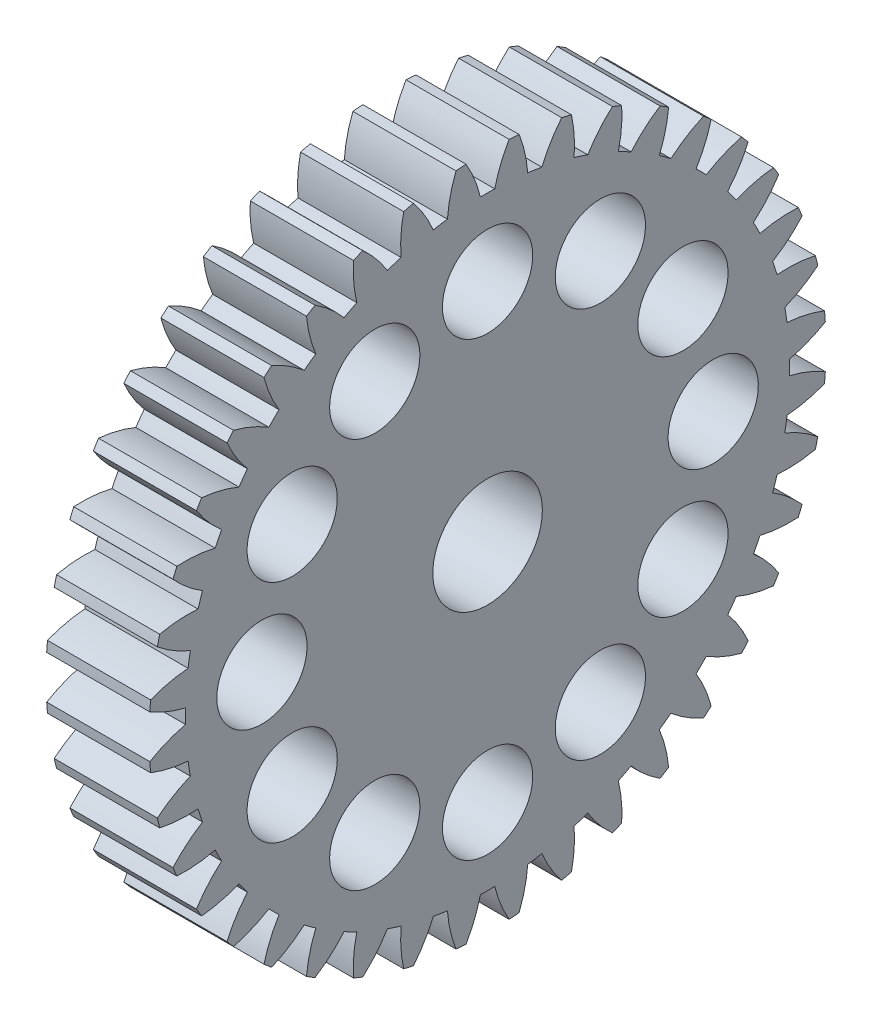
SolidWorks part; units mm, degrees
material "ПК/АБС"
ref_plane "Plane1" through (0, 0, 0) normal (0, 0, 1) x (1, 0, 0)
ref_plane "Plane2" through (0, 0, 0) normal (0, 1, 0) x (1, 0, 0)
ref_plane "Plane3" through (0, 0, 0) normal (1, 0, 0) x (0, 0, -1)
sketch "HoldingSke" plane through (0, 0, 0) normal (0, 1, 0) x (1, 0, 0)
  line L0 (0, 0) -> (0.6128, -0.5142)
  line L1 (-15, 0) -> (100, 0) construction
  line L2 (0, 0) -> (-2.1039, 2.3779)
  line L3 (0, 0) -> (-11.863, 4.5341)
  line L4 (0, 0) -> (6.6156, 5.5511)
  line L5 (0, 0) -> (-46.8476, -17.4728)
  line L6 (0, 0) -> (-6.6317, -4.4744)
  line L7 (-2.1039, 2.3779) -> (8.6586, 51.2059)
  line L8 (-76.2, 54.61) -> (-74.8, 54.61)
  line L9 (-71.009, 38.7566) -> (-53.1078, 45.2721)
  line L10 (-76.2, 71.12) -> (104.1128, 71.12)
  line L11 (0, 0) -> (-8, 0)
  line L12 (-76.2, 101.6) -> (-76.155, 101.6)
  line L13 (24.9733, 27.94) -> (52.9518, 28.4284)
  line L14 (24.9733, 27.94) -> (24.9743, 27.94)
  line L15 (24.9733, 27.94) -> (100.4006, 29.5858)
  line L16 (-63.627, -1.25) -> (-12.827, -1.25)
  circle A0 centre (0, 0) radius 4
  circle A1 centre (0, 0) radius 23.4365
  circle A2 centre (0, 0) radius 37.5
  circle A3 centre (0, 0) radius 4
  dimension "MHD" = 46.873
  dimension "Hub_dia" = 75
  dimension "Bore" = 8
  dimension "MBD" = 8
  dimension "Num_teeth" = 40
  dimension "Pitch" = 0.8
  dimension "Overall_len" = 50
  dimension "Show_teeth" = 40
  dimension "Thickness" = 8
  dimension "OAL" = 50.0001
  dimension "T_dim" = 1.4
  dimension "Ap" = 20
  dimension "H" = 19.05
  dimension "Pitch_radius" = 180.3128
  dimension "Width" = 8
  dimension "Backlash" = 0.045
  dimension "Addendum_fac" = 1
  dimension "Dedendum_fac" = 1.25
  dimension "Clearance_fac" = 0.25
  dimension "Dedendum_add" = 0.001
  dimension "Module" = 1.25
sketch "BasProSke" plane through (0, 0, 0) normal (0, 1, 0) x (1, 0, 0)
  line L0 (-10, 0) -> (60, 0) construction
  line L1 (0, 0) -> (0, 26.25)
  line L2 (0, 0) -> (8, 0)
  line L3 (8, 0) -> (8, 26.25)
  line L4 (8, 26.25) -> (0, 26.25)
  dimension "Thickness" = 8
  dimension "Diameter" = 52.5
revolve "Base-Revolve" add sketch "BasProSke" angle 360 about L0
sketch "TooCutSke" plane through (0, 0, 0) normal (1, 0, 0) x (0, 0, -1)
  line L1 (0, 0) -> (0, 107) construction
  line L2 (0, 0) -> (-1.0602, 24.9775) construction
  line L3 (0, 0) -> (-3.9204, 49.8134) construction
  line L4 (-1.0602, 24.9775) -> (-1.9602, 24.9067) construction
  arc A0 (0.5568, 23.4299) -> (-0.5568, 23.4299) centre (0, 0) ccw
  arc A1 (1.6852, 26.2213) -> (-1.6852, 26.2213) centre (0, 0) ccw
  circle A2 centre (0, 0) radius 25 construction
  circle A3 centre (0, 0) radius 23.4923 construction
  arc A4 (-0.5568, 23.4299) -> (-1.6852, 26.2213) centre (-10.2865, 21.1205) ccw
  arc A5 (1.6852, 26.2213) -> (0.5568, 23.4299) centre (10.2865, 21.1205) ccw
  dimension "Root_dia" = 46.873
  dimension "Overcut_dia" = 52.5508
  dimension "Pitch_dia" = 50
  dimension "Base_dia" = 46.9846
  dimension "Flank_rad" = 10
  dimension "Half_ang" = 4.5
  dimension "Half_CT" = 0.9027
extrude "ToothCut" cut sketch "TooCutSke" along normal through all
fillet "Breaks" [suppressed] radius 0.025
fillet "RootFillets" [suppressed] radius 0.3135
pattern_circular "TeethCuts" count 40 every 9 about axis through (-10, 0, 0) along (1, 0, 0) of "ToothCut", "RootFillets", "Breaks"
sketch "HubNeaOneSke" plane through (0, 0, 0) normal (-1, 0, 0) x (0, 0, 1)
  circle A0 centre (0, 0) radius 23.4365
  dimension "Diameter" = 46.873
extrude "HubNearOne" [suppressed] add sketch "HubNeaOneSke" along normal blind 42.0001
sketch "HubNeaBotSke" plane through (0, 0, 0) normal (-1, 0, 0) x (0, 0, 1)
  circle A0 centre (0, 0) radius 23.4365
  dimension "Diameter" = 46.873
extrude "HubNearBoth" [suppressed] add sketch "HubNeaBotSke" along normal blind 21
ref_plane "FarPln" through (8, 0, 0) normal (1, 0, 0) x (0, 0, -1)
sketch "HubFarSke" plane through (8, 0, 0) normal (1, 0, 0) x (0, 0, -1)
  circle A0 centre (0, 0) radius 23.4365
  dimension "Diameter" = 46.873
extrude "HubFar" [suppressed] add sketch "HubFarSke" along normal blind 21
sketch "BorSke" plane through (0, 0, 0) normal (1, 0, 0) x (0, 0, -1)
  circle A0 centre (0, 0) radius 4
  dimension "Diameter" = 8
extrude "Bore" cut sketch "BorSke" along normal mid plane 100.0001
sketch "KeySke" plane through (0, 0, 0) normal (1, 0, 0) x (0, 0, -1)
  line L0 (-1.5, 0) -> (-1.5, 5.4)
  line L1 (-1.5, 5.4) -> (1.5, 5.4)
  line L2 (1.5, 5.4) -> (1.5, 0)
  line L3 (0, 0) -> (0, 34) construction
  line L4 (-1.5, 0) -> (1.5, 0)
  dimension "Offset" = 5.4
  dimension "Width" = 3
extrude "Keyway" [suppressed] cut sketch "KeySke" along normal mid plane 100.0001
pattern_circular "Keyway2" [suppressed] count 2 every 90 about axis through (-10, 0, 0) along (1, 0, 0)
sketch "Эскиз1" plane through (8, 0, 0) normal (1, 0, 0) x (0, 0, -1)
  line L0 (0, 0) -> (0, 21) construction
  circle A0 centre (0, 0) radius 14
  circle A1 centre (0, 17.5) radius 3.5
  circle A2 centre (0, 0) radius 21
  point P6 (0, 0)
  dimension "D1" = 28
  dimension "D2" = 42
extrude "Вырез-Вытянуть1" cut sketch "Эскиз1" against normal through all both and the other way through all contours L0 A1 | A1 L0
pattern_circular "Круговой массив1" count 12 every 30 about axis through (0, 0, 0) along (1, 0, 0) of "Вырез-Вытянуть1"
sketch "Эскиз2" plane through (8, 0, 0) normal (1, 0, 0) x (0, 0, -1)
  circle A0 centre (0, 0) radius 4.25
  dimension "D1" = 8.5
extrude "Вырез-Вытянуть2" cut sketch "Эскиз2" against normal blind 10
equation "' \"Module@HoldingSke\" = 6.35"
equation "' \"Num_teeth@HoldingSke\" = 12"
equation "' \"Ap@HoldingSke\" =  20"
equation "' \"Ap@HoldingSke\" = 20"
equation "' \"Width@HoldingSke\" = 0.5 * 25.4"
equation "' \"Hub_dia@HoldingSke\"= 1 * 25.4"
equation "' \"Hub_dia@HoldingSke\" = 1 * 25.4"
equation "' \"Overall_len@HoldingSke\" = 1.0 * 25.4"
equation "' \"Bore@HoldingSke\" = 0.75 * 25.4"
equation "' \"T_dim@HoldingSke\" = 0.1 * 25.4"
equation "' \"Width@KeySke\" = 0.25 * 25.4"
equation "' \"Show_teeth@HoldingSke\" = 13"
equation "' \"Backlash@HoldingSke\" = 0.009 * 25.4"
equation "' \"Addendum_fac@HoldingSke\" = 1.0"
equation "' \"Dedendum_fac@HoldingSke\" = 1.25"
equation "' \"Dedendum_add@HoldingSke\" = 0.00005 * 25.4"
equation "' \"Clearance_fac@HoldingSke\" = 0.25"
equation "\"Pitch@HoldingSke\" = 1 / \"Module@HoldingSke\""
equation "\"Overcut_dia@TooCutSke\" = (\"Num_teeth@HoldingSke\" + 2 * \"Addendum_fac@HoldingSke\") / \"Pitch@HoldingSke\" + 0.002 * 25.4"
equation "\"Pitch_dia@TooCutSke\" = \"Num_teeth@HoldingSke\" / \"Pitch@HoldingSke\""
equation "\"Base_dia@TooCutSke\" = \"Num_teeth@HoldingSke\" / \"Pitch@HoldingSke\" * cos((\"Ap@HoldingSke\"  * 3.14159265 / 180))"
equation "\"Root_dia@TooCutSke\" = (\"Num_teeth@HoldingSke\" + 2) / \"Pitch@HoldingSke\" - 2 * (\"Addendum_fac@HoldingSke\" + \"Dedendum_fac@HoldingSke\") / \"Pitch@HoldingSke\" - \"Dedendum_add@HoldingSke\" * 2"
equation "\"Half_ang@TooCutSke\" = 180 / \"Num_teeth@HoldingSke\""
equation "\"Half_CT@TooCutSke\" = \"Num_teeth@HoldingSke\" / \"Pitch@HoldingSke\" * sin((3.14159265 / 2 / \"Num_teeth@HoldingSke\")) / 2 - 7 * \"Backlash@HoldingSke\" / 4"
equation "\"Flank_rad@TooCutSke\" = \"Num_teeth@HoldingSke\" / \"Pitch@HoldingSke\" / 5"
equation "\"Radius@RootFillets\" = \"Clearance_fac@HoldingSke\" / \"Pitch@HoldingSke\" + \"Dedendum_add@HoldingSke\""
equation "\"Break_rad@Breaks\" = 0.02 / \"Pitch@HoldingSke\""
equation "\"Thickness@HoldingSke\" = \"Width@HoldingSke\""
equation "\"OAL@HoldingSke\" = \"Thickness@HoldingSke\""
equation "\"MHD@HoldingSke\" = (\"Num_teeth@HoldingSke\" + 2) / \"Pitch@HoldingSke\" - 2 * (\"Addendum_fac@HoldingSke\" + \"Dedendum_fac@HoldingSke\")  / \"Pitch@HoldingSke\" - \"Dedendum_add@HoldingSke\" * 2"
equation "\"MBD@HoldingSke\" = (\"Num_teeth@HoldingSke\" + 2) / \"Pitch@HoldingSke\" - 2 * (\"Addendum_fac@HoldingSke\" + \"Dedendum_fac@HoldingSke\")  / \"Pitch@HoldingSke\" - \"Dedendum_add@HoldingSke\" * 2 - 0.002 * 25.4"
equation "\"MHD@HoldingSke\" = ((sgn( \"MHD@HoldingSke\" - \"Hub_dia@HoldingSke\" )-1)*( \"MHD@HoldingSke\" - \"Hub_dia@HoldingSke\" ))/-2+ \"Hub_dia@HoldingSke\""
equation "\"MBD@HoldingSke\" = ((sgn( \"MBD@HoldingSke\" - \"Bore@HoldingSke\" )-1)*( \"MBD@HoldingSke\" - \"Bore@HoldingSke\" ))/-2+ \"Bore@HoldingSke\""
equation "\"OAL@HoldingSke\" = ((sgn( \"OAL@HoldingSke\" - \"Overall_len@HoldingSke\" )+1)*( \"OAL@HoldingSke\" - \"Overall_len@HoldingSke\" ))/2 + \"Overall_len@HoldingSke\" + 0.000002 * 25.4"
equation "\"Num_teeth@TeethCuts\" = int( \"Show_teeth@HoldingSke\" ) + 1"
equation "\"Num_teeth@TeethCuts\" = ((sgn( \"Num_teeth@TeethCuts\" - \"Num_teeth@HoldingSke\" )-1)*( \"Num_teeth@TeethCuts\" - \"Num_teeth@HoldingSke\" ))/-2+ \"Num_teeth@HoldingSke\""
equation "\"Num_teeth@TeethCuts\" = ((sgn( \"Num_teeth@TeethCuts\" - 2.0)+1)*( \"Num_teeth@TeethCuts\" - 2.0))/2 +2.0"
equation "\"Angle@TeethCuts\" = 360.0 / \"Num_teeth@HoldingSke\""
equation "\"Diameter@BasProSke\" = (\"Num_teeth@HoldingSke\" + 2 * \"Addendum_fac@HoldingSke\") / \"Pitch@HoldingSke\""
equation "\"Thickness@BasProSke\"  = \"Thickness@HoldingSke\""
equation "' \"Fillet_rad@BasProSke\" =  \"Thickness@HoldingSke\" * 0.05"
equation "' \"Fillet_rad@BasProSke\" = \"Thickness@HoldingSke\" * 0.05"
equation "\"MHD@HoldingSke\" = ((sgn( \"MHD@HoldingSke\" - \"Root_dia@TooCutSke\" )-1)*( \"MHD@HoldingSke\" - \"Root_dia@TooCutSke\" ))/-2+ \"Root_dia@TooCutSke\""
equation "\"Diameter@HubNeaOneSke\" = \"MHD@HoldingSke\""
equation "\"Length@HubNearOne\" = \"OAL@HoldingSke\" - \"Thickness@BasProSke\""
equation "\"Diameter@HubNeaBotSke\" = \"MHD@HoldingSke\""
equation "\"Length@HubNearBoth\" = ( \"OAL@HoldingSke\" - \"Thickness@BasProSke\" ) / 2.0"
equation "\"Thickness@FarPln\" = \"Thickness@BasProSke\""
equation "\"Diameter@HubFarSke\" = \"MHD@HoldingSke\""
equation "\"Length@HubFar\" = ( \"OAL@HoldingSke\" - \"Thickness@BasProSke\" ) / 2.0"
equation "\"Diameter@BorSke\" = \"MBD@HoldingSke\""
equation "\"D1@Bore\" = \"OAL@HoldingSke\" * 2.0"
equation "\"D1@Keyway\" = \"OAL@HoldingSke\" * 2.0"
equation "\"Offset@KeySke\" = \"T_dim@HoldingSke\" + \"MBD@HoldingSke\" / 2.0"
